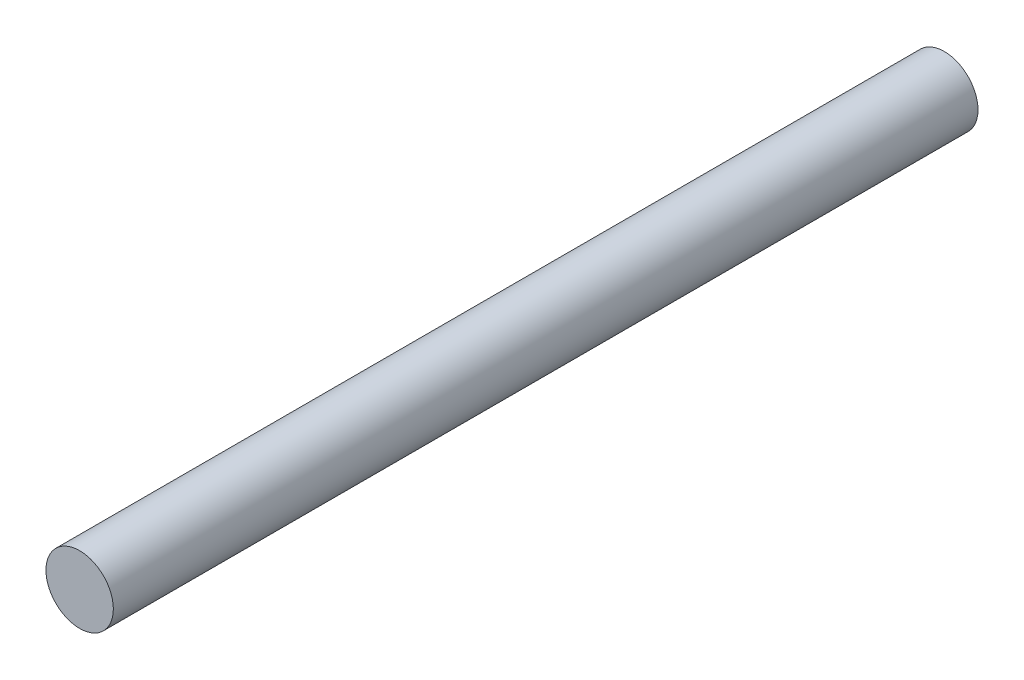
SolidWorks part; units mm, degrees
ref_plane "Front Plane" through (0, 0, 0) normal (0, 0, 1) x (1, 0, 0)
ref_plane "Top Plane" through (0, 0, 0) normal (0, 1, 0) x (1, 0, 0)
ref_plane "Right Plane" through (0, 0, 0) normal (1, 0, 0) x (0, 0, -1)
sketch "Sketch1" plane through (0, 0, 0) normal (0, 0, 1) x (1, 0, 0)
  line L1 (-2, 0) -> (2, 0) construction
  dimension "OD" = 4
sketch "Sketch2" plane through (0, 0, 0) normal (1, 0, 0) x (0, 0, -1)
  line L0 (25.4, 0) -> (-25.4, 0)
  point P4 (0, 0)
  dimension "Length" = 50.8
sketch "Sketch3" plane through (0, 0, 0) normal (0, 0, 1) x (1, 0, 0)
  circle A0 centre (0, 0) radius 2
extrude "Boss-Extrude1" add sketch "Sketch3" along normal blind 32.004 and the other way blind 19.304
